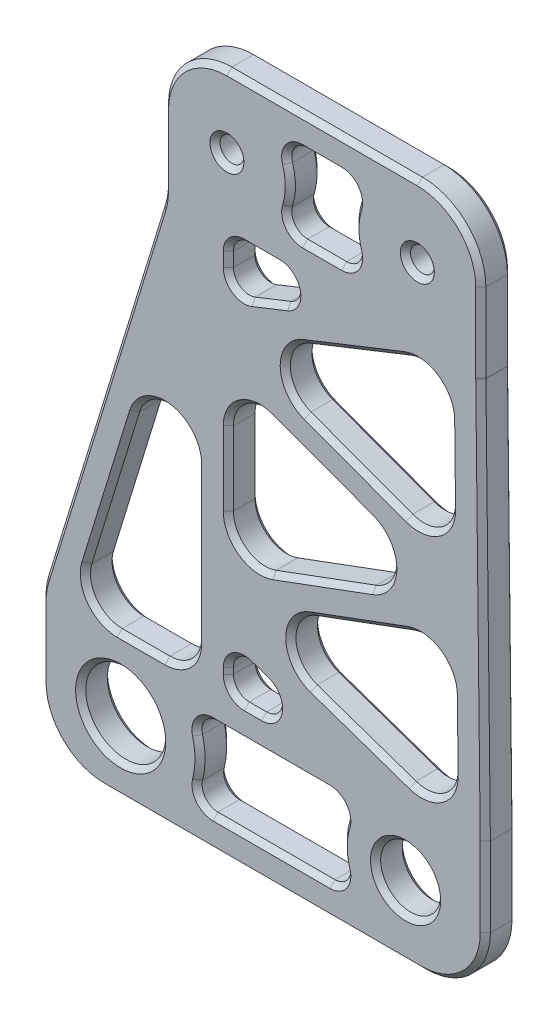
SolidWorks part; units mm, degrees
ref_plane "Front Plane" through (0, 0, 0) normal (0, 0, 1) x (1, 0, 0)
ref_plane "Top Plane" through (0, 0, 0) normal (0, 1, 0) x (1, 0, 0)
ref_plane "Right Plane" through (0, 0, 0) normal (1, 0, 0) x (0, 0, -1)
sketch "Sketch1" plane through (0, 0, 0) normal (0, 0, 1) x (1, 0, 0)
  line L0 (-15.875, 0) -> (15.875, 0)
  line L1 (-15.875, 0) -> (-15.875, -14.2875)
  line L2 (15.875, 0) -> (15.875, -14.2875)
  line L3 (-28.1254, -68.4124) -> (16.3246, -68.4124)
  line L4 (0, -68.4124) -> (0, 0) construction
  line L5 (-9.3783, -14.2875) -> (4.086, -14.2875)
  line L7 (3.4182, -54.1249) -> (-9.3783, -54.1249)
  line L8 (-28.1254, -54.1249) -> (-28.1254, -68.4124)
  line L12 (16.3246, -54.1249) -> (16.3246, -68.4124)
  line L13 (-4.568, -3.175) -> (4.568, -3.175)
  line L14 (16.3246, -61.2686) -> (8.349, -61.2686) construction
  line L15 (8.349, -61.2686) -> (-20.1498, -61.2686) construction
  line L16 (-20.1498, -61.2686) -> (-28.1254, -61.2686) construction
  line L17 (9.525, -7.1438) -> (-9.525, -7.1438) construction
  line L18 (15.875, -7.1438) -> (9.525, -7.1438) construction
  line L19 (-9.525, -7.1438) -> (-15.875, -7.1438) construction
  line L20 (-28.1254, -54.1249) -> (-15.875, -14.2875)
  line L21 (-24.8037, -54.1249) -> (-12.5533, -14.2875)
  line L22 (16.3246, -54.1249) -> (15.875, -14.2875)
  line L23 (13.1496, -54.1249) -> (12.9684, -38.0674)
  line L24 (-18.6785, -34.2062) -> (-21.7132, -33.273) construction
  line L25 (12.9303, -34.6955) -> (16.1053, -34.6955) construction
  line L26 (4.568, -11.1125) -> (-4.568, -11.1125)
  line L27 (-13.2757, -57.2999) -> (3.392, -57.2999)
  line L28 (-13.2757, -65.2374) -> (3.392, -65.2374)
  line L29 (-12.5533, -14.2875) -> (-12.5533, -54.1249)
  line L30 (-9.3783, -14.2875) -> (-9.3783, -19.6261)
  line L31 (-9.3783, -34.2062) -> (-12.5533, -34.2062) construction
  line L32 (13.1496, -54.1249) -> (-9.3783, -46.3493)
  line L33 (-9.3783, -46.3493) -> (12.9684, -38.0674)
  line L35 (12.7, -14.2875) -> (-9.3783, -23.0416)
  line L36 (-9.3783, -23.0416) -> (12.8919, -31.2952)
  line L38 (-9.3783, -26.4276) -> (12.9303, -34.6955)
  line L39 (12.9303, -34.6955) -> (-9.3783, -42.9633)
  line L40 (-9.3783, -19.6261) -> (4.086, -14.2875)
  line L41 (-9.3783, -49.7081) -> (3.4182, -54.1249)
  line L42 (-2.98, -51.9165) -> (-1.9441, -48.9152) construction
  line L43 (-2.6461, -16.9568) -> (-1.4759, -19.9083) construction
  line L44 (1.795, -42.2084) -> (0.6917, -39.2313) construction
  line L45 (1.7568, -27.1684) -> (0.6535, -30.1455) construction
  line L46 (-9.3783, -26.4276) -> (-9.3783, -42.9633)
  line L47 (-9.3783, -49.7081) -> (-9.3783, -54.1249)
  line L48 (-12.5533, -54.1249) -> (-24.8037, -54.1249)
  line L49 (12.8919, -31.2952) -> (12.7, -14.2875)
  circle A0 centre (-20.1498, -61.2686) radius 4
  circle A1 centre (8.349, -61.2686) radius 3
  circle A2 centre (-9.525, -7.1438) radius 1.1906
  circle A3 centre (9.525, -7.1438) radius 1.1906
  arc A4 (-4.568, -11.1125) -> (-4.568, -3.175) centre (-9.525, -7.1438) ccw
  arc A5 (4.568, -3.175) -> (4.568, -11.1125) centre (9.525, -7.1438) ccw
  arc A6 (-13.2757, -65.2374) -> (-13.2757, -57.2999) centre (-20.1498, -61.2686) ccw
  arc A7 (3.392, -57.2999) -> (3.392, -65.2374) centre (8.349, -61.2686) ccw
  point P23 (-5.9004, -61.2686)
  point P27 (0, -7.1438)
  dimension "D7" = 8
  dimension "D8" = 6
  dimension "D11" = 2.3813
  dimension "D6" = 12.7
  dimension "D16" = 15.875
  dimension "D17" = 12.7
  dimension "D1" = 31.75
  dimension "D2" = 14.2875
  dimension "D3" = 44.45
  dimension "D4" = 54.1249
  dimension "D5" = 14.2875
  dimension "D9" = 28.4988
  dimension "D10" = 19.05
  dimension "D12" = 5.9004
  dimension "D13" = 3.175
  dimension "D14" = 3.175
  dimension "D15" = 3.175
  dimension "D18" = 3.175
  dimension "D19" = 3.175
extrude "Boss-Extrude1" add sketch "Sketch1" along normal mid plane 3.175 contours L7 L8 L3 L12 L2 L0 L1 L5
fillet "Fillet1" radius 6.35 7 edges at (16.3246, -68.4124, 0) (-28.1254, -68.4124, 0) (15.875, 0, 0) (-15.875, 0, 0) (15.875, -14.2875, 0) (-28.1254, -54.1249, 0) (-15.875, -14.2875, 0)
fillet "Fillet3" radius 3.175 12 edges at (-24.8037, -54.1249, 0) (-12.5533, -54.1249, 0) (-12.5533, -14.2875, 0) (-9.3783, -46.3493, 0) (13.1496, -54.1249, 0) (12.9684, -38.0674, 0) (12.8919, -31.2952, 0) (12.7, -14.2875, 0) (-9.3783, -23.0416, 0) (-9.3783, -26.4276, 0) (12.9303, -34.6955, 0) (-9.3783, -42.9633, 0)
fillet "Fillet2" radius 1.5875 14 edges at (4.568, -11.1125, 0) (4.568, -3.175, 0) (-4.568, -11.1125, 0) (-4.568, -3.175, 0) (3.392, -65.2374, 0) (3.392, -57.2999, 0) (-13.2757, -65.2374, 0) (-13.2757, -57.2999, 0) (-9.3783, -49.7081, 0) (-9.3783, -54.1249, 0) (3.4182, -54.1249, 0) (-9.3783, -14.2875, 0) (-9.3783, -19.6261, 0) (4.086, -14.2875, 0)
chamfer "Chamfer1" distance 0.508 angle 45 142 edges at (10.7156, -7.1438, -1.5875) (-8.3344, -7.1438, -1.5875) (11.349, -61.2686, -1.5875) (-16.1498, -61.2686, -1.5875) (14.0151, -1.8599, -1.5875) (0, 0, -1.5875) (-14.0151, -1.8599, -1.5875) (-15.875, -9.8416, -1.5875) (-6.9189, -54.1249, -1.5875) (-28.1254, -58.5708, -1.5875) (-26.2655, -66.5525, -1.5875) (-5.9004, -68.4124, -1.5875) (14.4647, -66.5525, -1.5875) (16.3246, -58.0936, -1.5875) (15.875, -10.3008, -1.5875) (10.7156, -7.1438, 1.5875) (11.349, -61.2686, 1.5875) (16.3246, -58.0936, 1.5875) (14.4647, -66.5525, 1.5875) (-5.9004, -68.4124, 1.5875) (-26.2655, -66.5525, 1.5875) (-28.1254, -58.5708, 1.5875) (-6.9189, -54.1249, 1.5875) (-15.875, -9.8416, 1.5875) (-14.0151, -1.8599, 1.5875) (0, 0, 1.5875) (14.0151, -1.8599, 1.5875) (15.875, -10.3008, 1.5875) (-16.1498, -61.2686, 1.5875) (-8.3344, -7.1438, 1.5875) (-6.0077, -14.2875, -1.5875) (13.059, -46.0961, -1.5875) (-21.1517, -42.2489, -1.5875) (-22.0002, -34.2062, -1.5875) (16.1, -34.2241, -1.5875) (13.059, -46.0961, 1.5875) (-6.0077, -14.2875, 1.5875) (-21.1517, -42.2489, 1.5875) (16.1, -34.2241, 1.5875) (-22.0002, -34.2062, 1.5875) (-15.9455, -14.2769, -1.5875) (-28.0549, -54.1355, -1.5875) (15.8751, -14.2875, -1.5875) (15.8751, -14.2875, 1.5875) (-28.0549, -54.1355, 1.5875) (-15.9455, -14.2769, 1.5875) (0, -3.175, -1.5875) (3.175, -7.1438, -1.5875) (0, -11.1125, -1.5875) (-3.175, -7.1438, -1.5875) (3.175, -7.1438, 1.5875) (0, -3.175, 1.5875) (-3.175, -7.1438, 1.5875) (0, -11.1125, 1.5875) (2.057, -57.9482, -1.5875) (1.999, -61.2686, -1.5875) (2.057, -64.589, -1.5875) (-5.0751, -65.2374, -1.5875) (-12.1823, -64.622, -1.5875) (-12.2123, -61.2686, -1.5875) (-12.1823, -57.9152, -1.5875) (-5.0751, -57.2999, -1.5875) (3.233, -3.8233, -1.5875) (3.233, -10.4642, -1.5875) (-3.233, -10.4642, -1.5875) (-3.233, -3.8233, -1.5875) (2.057, -64.589, 1.5875) (1.999, -61.2686, 1.5875) (2.057, -57.9482, 1.5875) (-5.0751, -57.2999, 1.5875) (-12.1823, -57.9152, 1.5875) (-12.2123, -61.2686, 1.5875) (-12.1823, -64.622, 1.5875) (-5.0751, -65.2374, 1.5875) (3.233, -10.4642, 1.5875) (3.233, -3.8233, 1.5875) (-3.233, -3.8233, 1.5875) (-3.233, -10.4642, 1.5875) (-6.4009, -50.7358, -1.5875) (-9.3783, -52.2364, -1.5875) (-9.3783, -34.6955, -1.5875) (-0.1013, -29.8658, -1.5875) (-0.1013, -39.5251, -1.5875) (3.8414, -41.45, -1.5875) (3.9486, -50.9491, -1.5875) (-12.5533, -43.1821, -1.5875) (-18.1169, -54.1249, -1.5875) (-5.4226, -18.0577, -1.5875) (-9.3783, -16.582, -1.5875) (3.4732, -27.8045, -1.5875) (3.3624, -17.9899, -1.5875) (12.796, -22.7914, -1.5875) (-6.4009, -50.7358, 1.5875) (-9.3783, -52.2364, 1.5875) (-9.3783, -34.6955, 1.5875) (-0.1013, -39.5251, 1.5875) (-0.1013, -29.8658, 1.5875) (3.4732, -27.8045, 1.5875) (12.796, -22.7914, 1.5875) (3.3624, -17.9899, 1.5875) (3.8414, -41.45, 1.5875) (3.9486, -50.9491, 1.5875) (-18.1169, -54.1249, 1.5875) (-12.5533, -43.1821, 1.5875) (-9.3783, -16.582, 1.5875) (-5.4226, -18.0577, 1.5875) (-4.4813, -52.7999, -1.5875) (-8.9133, -53.6599, -1.5875) (-8.7122, -50.6427, -1.5875) (-8.0168, -28.3842, -1.5875) (6.969, -34.6955, -1.5875) (-8.0168, -41.0067, -1.5875) (11.6432, -39.9949, -1.5875) (11.7812, -52.2278, -1.5875) (-3.1298, -46.2788, -1.5875) (-15.2564, -32.2746, -1.5875) (-13.4832, -53.1949, -1.5875) (-23.0594, -52.8363, -1.5875) (-2.6654, -15.5771, -1.5875) (-8.6828, -18.6022, -1.5875) (-8.9133, -14.7525, -1.5875) (-3.6867, -22.9774, -1.5875) (11.3464, -16.3047, -1.5875) (11.4932, -29.3091, -1.5875) (-4.4813, -52.7999, 1.5875) (-8.7122, -50.6427, 1.5875) (-8.9133, -53.6599, 1.5875) (-8.0168, -28.3842, 1.5875) (-8.0168, -41.0067, 1.5875) (6.969, -34.6955, 1.5875) (-3.6867, -22.9774, 1.5875) (11.4932, -29.3091, 1.5875) (11.3464, -16.3047, 1.5875) (11.6432, -39.9949, 1.5875) (-3.1298, -46.2788, 1.5875) (11.7812, -52.2278, 1.5875) (-15.2564, -32.2746, 1.5875) (-23.0594, -52.8363, 1.5875) (-13.4832, -53.1949, 1.5875) (-2.6654, -15.5771, 1.5875) (-8.9133, -14.7525, 1.5875) (-8.6828, -18.6022, 1.5875)
